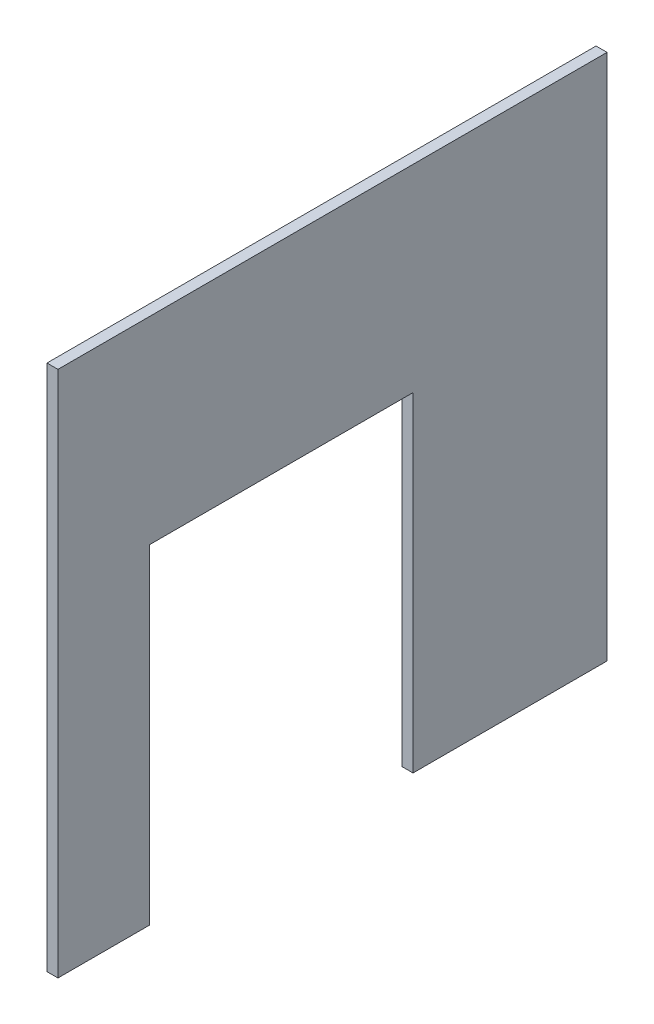
SolidWorks part; units mm, degrees
ref_plane "Front Plane" through (0, 0, 0) normal (0, 0, 1) x (1, 0, 0)
ref_plane "Top Plane" through (0, 0, 0) normal (0, 1, 0) x (1, 0, 0)
ref_plane "Right Plane" through (0, 0, 0) normal (1, 0, 0) x (0, 0, -1)
sketch "Sketch1" plane through (0, 0, 0) normal (1, 0, 0) x (0, 0, -1)
  line L0 (0, 0) -> (50, 0)
  line L2 (0, 0) -> (0, 288)
  line L3 (0, 288) -> (300, 288)
  line L4 (300, 0) -> (300, 288)
  line L5 (50, 0) -> (50, 180)
  line L6 (50, 180) -> (194, 180)
  line L7 (194, 180) -> (194, 0)
  line L8 (194, 0) -> (300, 0)
  dimension "D1" = 300
  dimension "D2" = 288
  dimension "D3" = 144
  dimension "D4" = 300
  dimension "D5" = 288
  dimension "D6" = 180
extrude "Boss-Extrude1" add sketch "Sketch1" along normal blind 6
